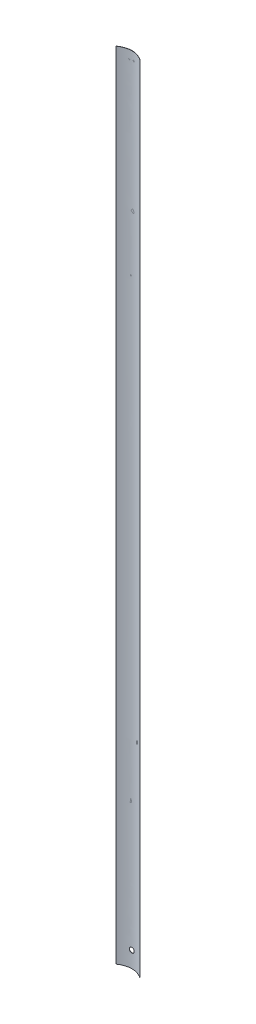
SolidWorks part; units mm, degrees
ref_plane "Front Plane" through (0, 0, 0) normal (0, 0, 1) x (1, 0, 0)
ref_plane "Top Plane" through (0, 0, 0) normal (0, 1, 0) x (1, 0, 0)
ref_plane "Right Plane" through (0, 0, 0) normal (1, 0, 0) x (0, 0, -1)
sketch "Sketch1" plane through (0, 0, 0) normal (0, 1, 0) x (1, 0, 0)
  line L0 (7.55, -2.55) -> (7.45, -2.55)
  line L1 (-7.45, -2.55) -> (-7.55, -2.55)
  spline S0 degree 2 poles (7.55, -2.55) (0, 2.55) (-7.55, -2.55) knots 0 0 0 1 1 1
  spline S1 degree 2 poles (-7.45, -2.55) (0, 2.35) (7.45, -2.55) knots 0 0 0 1 1 1
  dimension "D1" = 7.45
  dimension "D2" = 7.45
  dimension "D3" = 2.45
  dimension "D4" = 2.55
  dimension "D5" = 0.1
  dimension "D6" = 7.55
extrude "Boss-Extrude1" add sketch "Sketch1" along normal blind 495
sketch "Sketch2" plane through (0, 0, 0) normal (0, 0, 1) x (1, 0, 0)
  circle A0 centre (0, 10) radius 1.5
  dimension "D1" = 3
  dimension "D2" = 10
extrude "Cut-Extrude4" cut sketch "Sketch2" along normal through all
